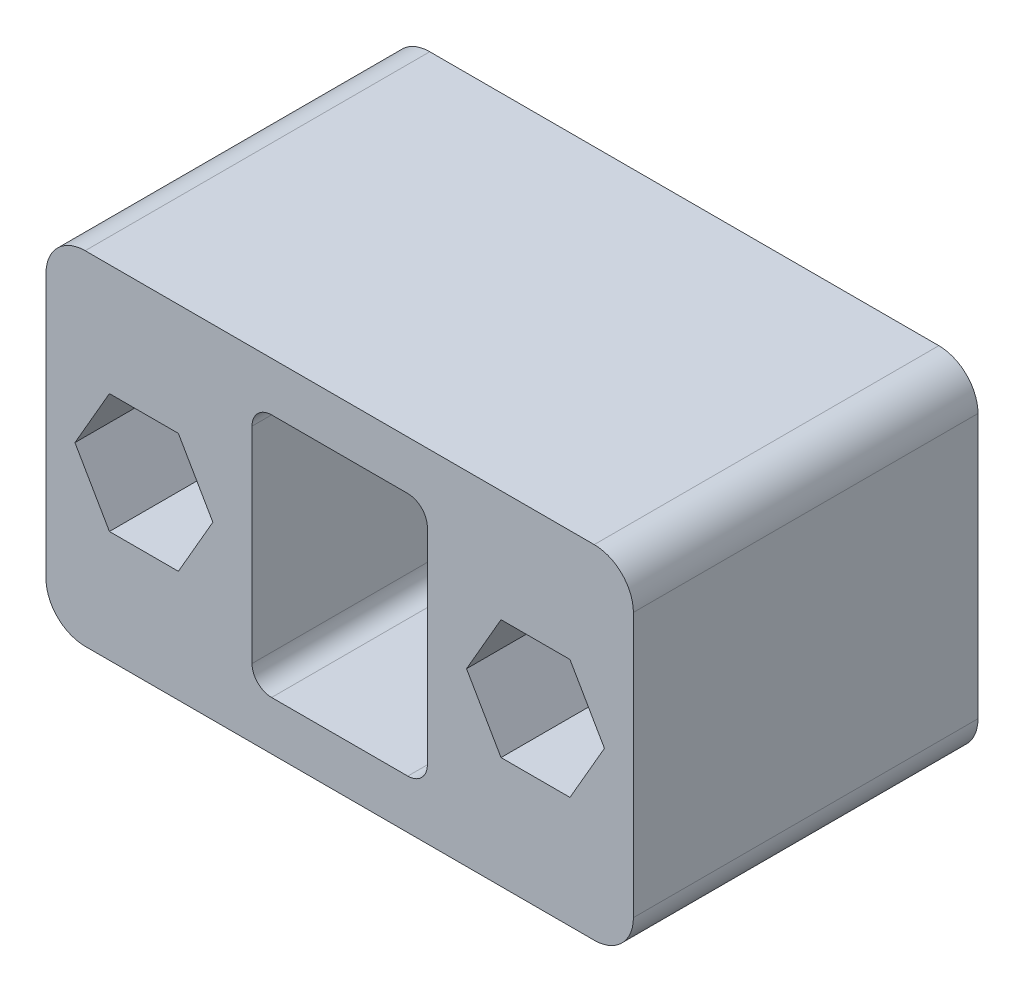
SolidWorks part; units mm, degrees
ref_plane "前视基准面" through (0, 0, 0) normal (0, 0, 1) x (1, 0, 0)
ref_plane "上视基准面" through (0, 0, 0) normal (0, 1, 0) x (1, 0, 0)
ref_plane "右视基准面" through (0, 0, 0) normal (1, 0, 0) x (0, 0, -1)
other "Configuration Table"
sketch "草图1" plane through (0, 0, 0) normal (0, 0, 1) x (1, 0, 0)
  line L0 (-10, 0) -> (10, 0) construction
  line L1 (-15, -8.75) -> (15, -8.75)
  line L2 (-15, -8.75) -> (-15, 8.75)
  line L3 (-15, 8.75) -> (15, 8.75)
  line L4 (15, -8.75) -> (15, 8.75)
  line L5 (-15, -8.75) -> (15, 8.75) construction
  line L6 (-15, 8.75) -> (15, -8.75) construction
  line L8 (11.7609, 3.05) -> (8.2391, 3.05)
  line L9 (8.2391, 3.05) -> (6.4782, 0)
  line L10 (6.4782, 0) -> (8.2391, -3.05)
  line L11 (8.2391, -3.05) -> (11.7609, -3.05)
  line L12 (11.7609, -3.05) -> (13.5218, 0)
  line L13 (13.5218, 0) -> (11.7609, 3.05)
  line L14 (-11.7609, 3.05) -> (-13.5218, 0)
  line L15 (-13.5218, 0) -> (-11.7609, -3.05)
  line L16 (-11.7609, -3.05) -> (-8.2391, -3.05)
  line L17 (-8.2391, -3.05) -> (-6.4782, 0)
  line L18 (-6.4782, 0) -> (-8.2391, 3.05)
  line L19 (-8.2391, 3.05) -> (-11.7609, 3.05)
  line L22 (-4.4782, -6.25) -> (4.4782, -6.25)
  line L23 (-4.4782, -6.25) -> (-4.4782, 6.25)
  line L24 (-4.4782, 6.25) -> (4.4782, 6.25)
  line L25 (4.4782, -6.25) -> (4.4782, 6.25)
  line L26 (-4.4782, -6.25) -> (4.4782, 6.25) construction
  line L27 (-4.4782, 6.25) -> (4.4782, -6.25) construction
  circle A0 centre (10, 0) radius 3.05 construction
  circle A1 centre (-10, 0) radius 3.05 construction
  point P0 (0, 0)
  point P6 (0, 0)
  point P9 (0, 0)
  dimension "D5" = 2.5
  dimension "D1" = 17.5
  dimension "D2" = 20
  dimension "D3" = 6.1
  dimension "D4" = 5
  dimension "D6" = 2
extrude "凸台-拉伸1" add sketch "草图1" along normal blind 17.6
fillet "圆角1" radius 1 4 edges at (4.4782, 6.25, 8.8) (-4.4782, -6.25, 8.8) (4.4782, -6.25, 8.8) (-4.4782, 6.25, 8.8)
sketch "草图3" plane through (0, 0, 0) normal (0, 0, -1) x (-1, 0, 0)
  line L0 (15, -8.75) -> (-15, -8.75) construction
  line L1 (-15, 8.75) -> (-4.4782, 8.75)
  line L2 (-15, 8.75) -> (-15, -8.75)
  line L3 (-15, -8.75) -> (-4.4782, -8.75)
  line L4 (-4.4782, 8.75) -> (-4.4782, -8.75)
  line L5 (-15, 8.75) -> (15, 8.75) construction
  line L6 (15, -8.75) -> (4.4782, -8.75)
  line L7 (15, -8.75) -> (15, 8.75)
  line L8 (15, 8.75) -> (4.4782, 8.75)
  line L9 (4.4782, -8.75) -> (4.4782, 8.75)
  line L10 (4.4782, 5.25) -> (4.4782, -5.25) construction
  line L11 (-4.4782, -5.25) -> (-4.4782, 5.25) construction
extrude "凸台-拉伸2" add sketch "草图3" against normal offset from surface (2.1 mm away) 15.5 up to face at (-10, 0, 17.6)
fillet "圆角2" radius 2 4 edges at (15, -8.75, 8.8) (-15, -8.75, 8.8) (-15, 8.75, 8.8) (15, 8.75, 8.8)
sketch "草图4" plane through (0, 0, 2.1) normal (0, 0, 1) x (1, 0, 0)
  line L0 (-10, 0) -> (10, 0) construction
  circle A0 centre (10, 0) radius 2.1
  circle A1 centre (-10, 0) radius 2.1
  point P4 (0, 0)
  dimension "D1" = 4.2
  dimension "D2" = 20
extrude "切除-拉伸1" cut sketch "草图4" against normal blind 10
